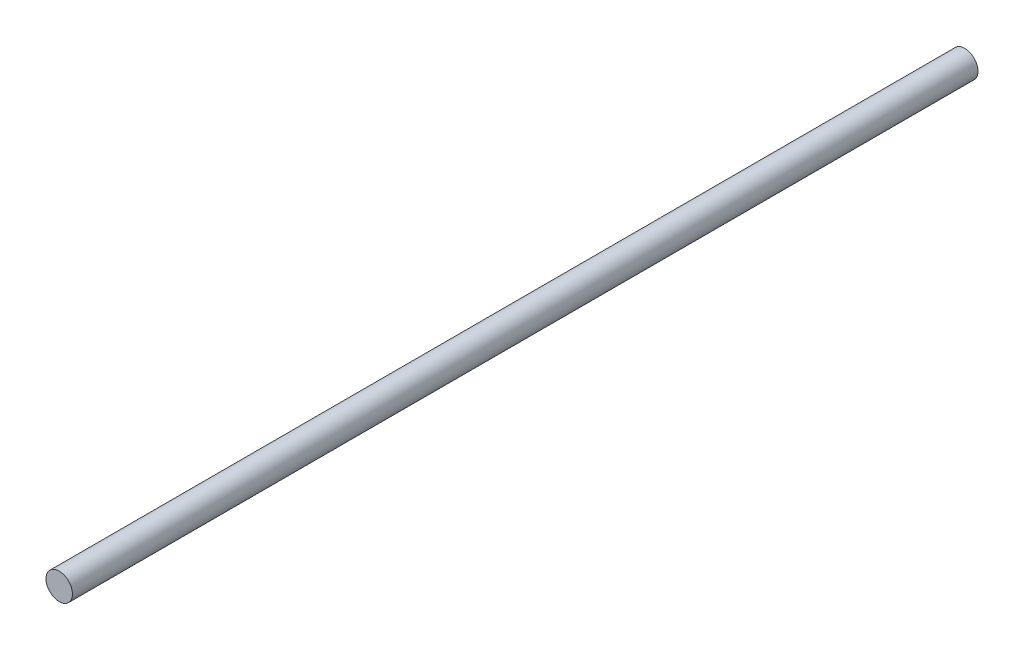
SolidWorks part; units mm, degrees
ref_plane "Front" through (0, 0, 0) normal (0, 0, 1) x (1, 0, 0)
ref_plane "Top" through (0, 0, 0) normal (0, 1, 0) x (1, 0, 0)
ref_plane "Right" through (0, 0, 0) normal (1, 0, 0) x (0, 0, -1)
sketch "Sketch1" plane through (0, 0, 0) normal (0, 0, 1) x (1, 0, 0)
  circle A0 centre (0, 0) radius 2.5
  dimension "D1" = 5
extrude "Boss-Extrude1" add sketch "Sketch1" against normal blind 171
